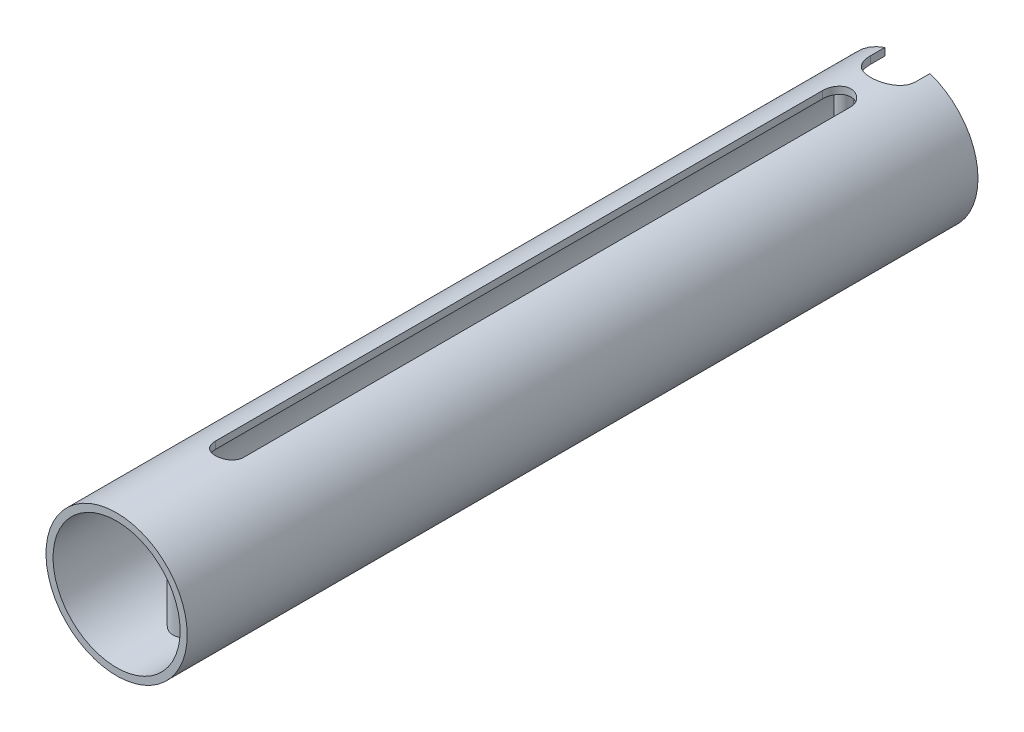
SolidWorks part; units mm, degrees
material "Laiton"
ref_plane "Plan de face" through (0, 0, 0) normal (0, 0, 1) x (1, 0, 0)
ref_plane "Plan de dessus" through (0, 0, 0) normal (0, 1, 0) x (1, 0, 0)
ref_plane "Plan de droite" through (0, 0, 0) normal (1, 0, 0) x (0, 0, -1)
sketch "Esquisse1" plane through (0, 0, 0) normal (0, 0, 1) x (1, 0, 0)
  circle A0 centre (0, 0) radius 4.5
  circle A1 centre (0, 0) radius 5
  dimension "D2" = 10
  dimension "D3" = 0.5
extrude "Boss.-Extru.1" add sketch "Esquisse1" along normal mid plane 56
sketch "Esquisse2" plane through (0, 0, 0) normal (0, 1, 0) x (1, 0, 0)
  line L0 (5, 28) -> (-5, 28) construction
  line L1 (-5, -28) -> (5, -28) construction
  circle A0 centre (0, -23) radius 1
  circle A1 centre (-3, 26.5) radius 0.5
  dimension "D1" = 2
  dimension "D5" = 1
  dimension "D2" = 5
  dimension "D3" = 1.5
  dimension "D4" = 3
extrude "Boss.-Extru.2" add sketch "Esquisse2" along normal up to next and the other way up to next
sketch "Esquisse3" plane through (0, 0, 0) normal (0, 1, 0) x (1, 0, 0)
  line L0 (0, 23) -> (0, -20) construction
  line L1 (1, 23) -> (1, -20)
  line L2 (-1, 23) -> (-1, -20)
  line L3 (4.5, 28) -> (-4.5, 28) construction
  arc A0 (1, 23) -> (-1, 23) centre (0, 23) ccw
  arc A1 (-1, -20) -> (1, -20) centre (0, -20) ccw
  circle A4 centre (0, -23) radius 1 construction
  point P3 (0, 1.5)
  dimension "D2" = 3
  dimension "D1" = 2
  dimension "D3" = 5
extrude "Enlèv. mat.-Extru.1" cut sketch "Esquisse3" against normal through all and the other way through all
sketch "Esquisse4" plane through (0, 0, 0) normal (0, 1, 0) x (1, 0, 0)
  line L0 (0, 27) -> (0, 28) construction
  line L1 (-1.6, 27) -> (-1.6, 28)
  line L2 (1.6, 27) -> (1.6, 28)
  line L3 (4.5, 28) -> (-4.5, 28) construction
  arc A0 (-1.6, 27) -> (1.6, 27) centre (0, 27) ccw
  arc A1 (1.6, 28) -> (-1.6, 28) centre (0, 28) ccw
  point P4 (0, 27.5)
  dimension "D2" = 1.6
  dimension "D1" = 1
extrude "Enlèv. mat.-Extru.2" cut sketch "Esquisse4" against normal through all and the other way through all
